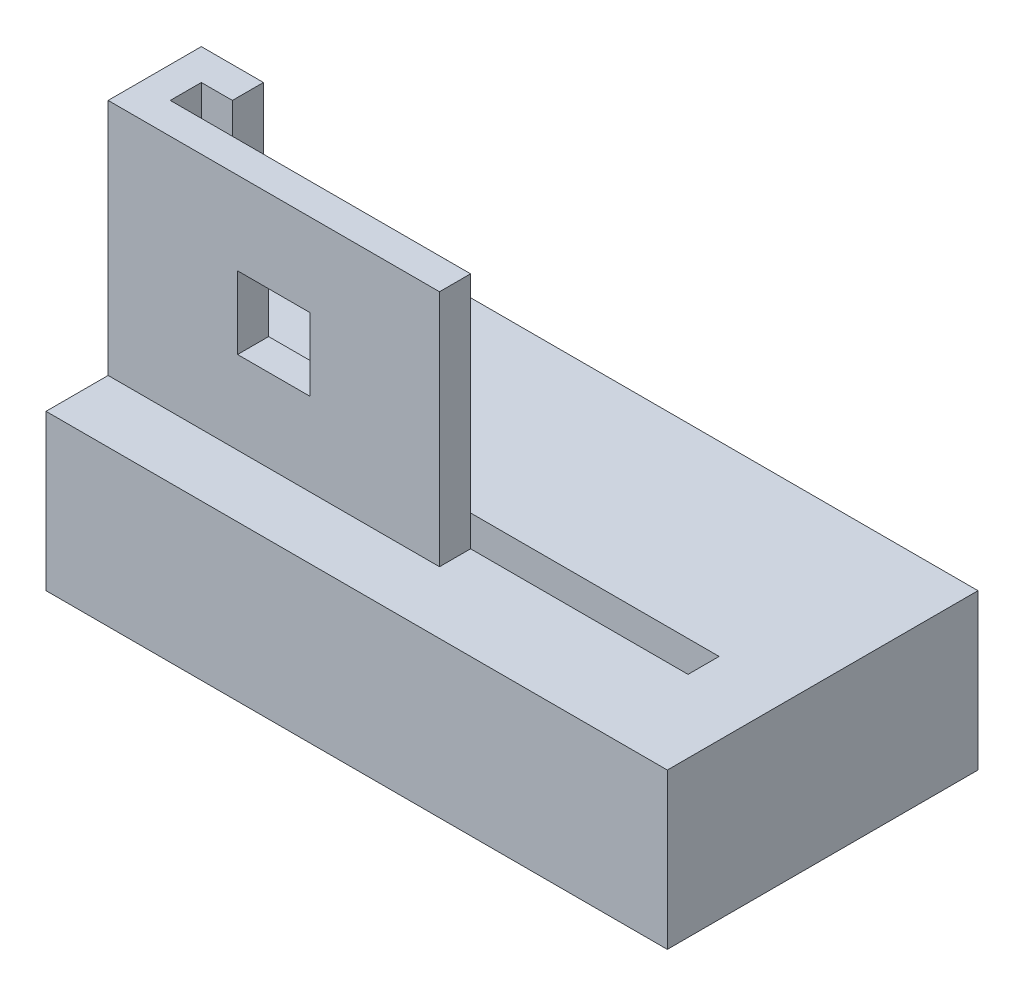
SolidWorks part; units mm, degrees
ref_plane "Plan de face" through (0, 0, 0) normal (0, 0, 1) x (1, 0, 0)
ref_plane "Plan de dessus" through (0, 0, 0) normal (0, 1, 0) x (1, 0, 0)
ref_plane "Plan de droite" through (0, 0, 0) normal (1, 0, 0) x (0, 0, -1)
sketch "Esquisse5" plane through (0, 0, 0) normal (0, 1, 0) x (1, 0, 0)
  line L1 (0, 0) -> (-60, 0)
  line L2 (0, 0) -> (0, -30)
  line L3 (0, -30) -> (-60, -30)
  line L4 (-60, 0) -> (-60, -30)
  dimension "D1" = 30
  dimension "D2" = 60
extrude "Boss.-Extru.2" add sketch "Esquisse5" along normal blind 15 contours L3 L4 L1 L2
sketch "Esquisse6" plane through (0, 0, 0) normal (0, -1, 0) x (1, 0, 0)
  line L0 (0, 15) -> (-60, 15) construction
  line L1 (0, 0) -> (0, 30) construction
  line L2 (-60, 0) -> (-60, 30) construction
  circle A0 centre (-55, 15) radius 5
  circle A1 centre (-15, 15) radius 5
  point P6 (-55, 15)
  point P7 (-15, 15)
  dimension "D3" = 10
  dimension "D4" = 10
  dimension "D1" = 5
  dimension "D2" = 40
extrude "Boss.-Extru.3" add sketch "Esquisse6" along normal blind 6
sketch "Esquisse7" plane through (0, 15, 0) normal (0, 1, 0) x (1, 0, 0)
  line L0 (-60, 0) -> (-60, -30) construction
  line L1 (-60, -15) -> (-54, -15)
  line L2 (-54, -15) -> (-54, -18)
  line L3 (-54, -18) -> (-57, -18)
  line L4 (-57, -18) -> (-57, -21)
  line L5 (-57, -21) -> (-28, -21)
  line L6 (-28, -21) -> (-28, -24)
  line L7 (-28, -24) -> (-60, -24)
  line L12 (0, -30) -> (0, 0)
  line L13 (0, 0) -> (-60, 0)
  line L14 (-60, 0) -> (-60, -30)
  line L15 (-60, -30) -> (0, -30)
  line L18 (-60, -15) -> (-60, -24)
  point P0 (-60, -15)
  dimension "D1" = 3
  dimension "D2" = 3
  dimension "D3" = 3
  dimension "D4" = 6
  dimension "D5" = 3
  dimension "D6" = 32
  dimension "D7" = 0
extrude "Boss.-Extru.4" add sketch "Esquisse7" along normal blind 23
sketch "Esquisse8" plane through (0, 15, 0) normal (0, 1, 0) x (1, 0, 0)
  line L1 (-57, -18) -> (-7, -18)
  line L2 (-57, -18) -> (-57, -21)
  line L3 (-57, -21) -> (-7, -21)
  line L4 (-7, -18) -> (-7, -21)
  dimension "D1" = 3
  dimension "D2" = 50
extrude "Enlèv. mat.-Extru.1" cut sketch "Esquisse8" against normal blind 7
sketch "Esquisse9" plane through (0, 0, 24) normal (0, 0, 1) x (1, 0, 0)
  line L0 (-60, 38) -> (-28, 15) construction
  line L2 (-47.5, 23) -> (-40.5, 23)
  line L3 (-47.5, 23) -> (-47.5, 30)
  line L4 (-47.5, 30) -> (-40.5, 30)
  line L5 (-40.5, 23) -> (-40.5, 30)
  line L6 (-47.5, 23) -> (-40.5, 30) construction
  line L7 (-47.5, 30) -> (-40.5, 23) construction
  point P4 (-44, 26.5)
  dimension "D1" = 7
  dimension "D2" = 7
extrude "Enlèv. mat.-Extru.2" cut sketch "Esquisse9" against normal blind 7
